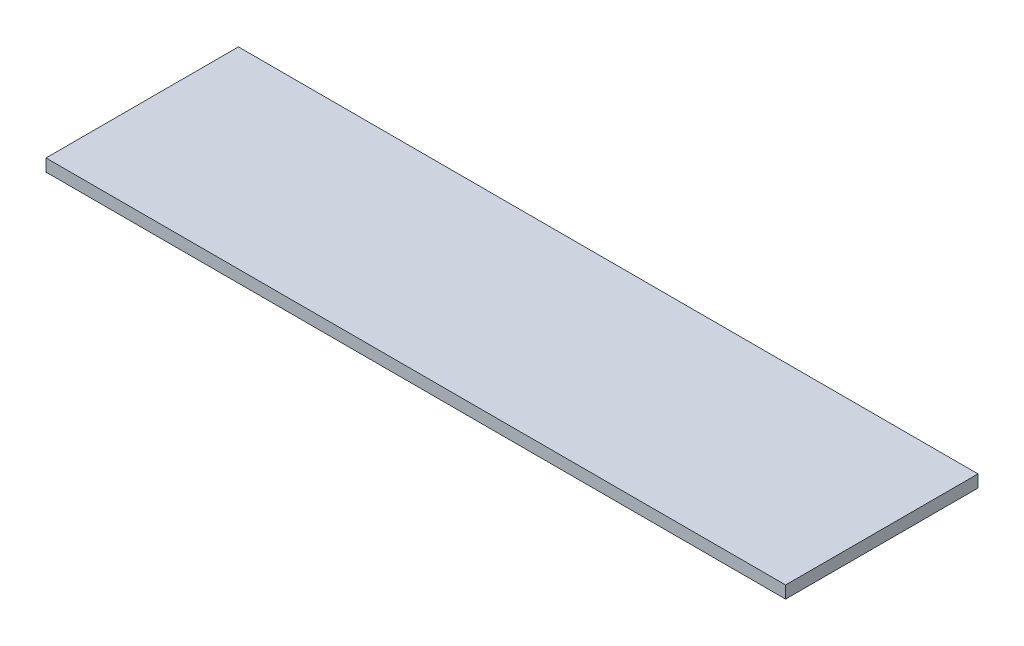
SolidWorks part; units mm, degrees
ref_plane "Спереди" through (0, 0, 0) normal (0, 0, 1) x (1, 0, 0)
ref_plane "Сверху" through (0, 0, 0) normal (0, 1, 0) x (1, 0, 0)
ref_plane "Справа" through (0, 0, 0) normal (1, 0, 0) x (0, 0, -1)
sketch "Эскиз1" plane through (0, 0, 0) normal (0, 1, 0) x (1, 0, 0)
  line L1 (542, -141) -> (-542, -141)
  line L2 (542, -141) -> (542, 141)
  line L3 (542, 141) -> (-542, 141)
  line L4 (-542, -141) -> (-542, 141)
  line L5 (542, -141) -> (-542, 141) construction
  line L6 (542, 141) -> (-542, -141) construction
  point P0 (0, 0)
  dimension "D1" = 1084
  dimension "D2" = 282
extrude "Бобышка-Вытянуть1" add sketch "Эскиз1" along normal blind 18
